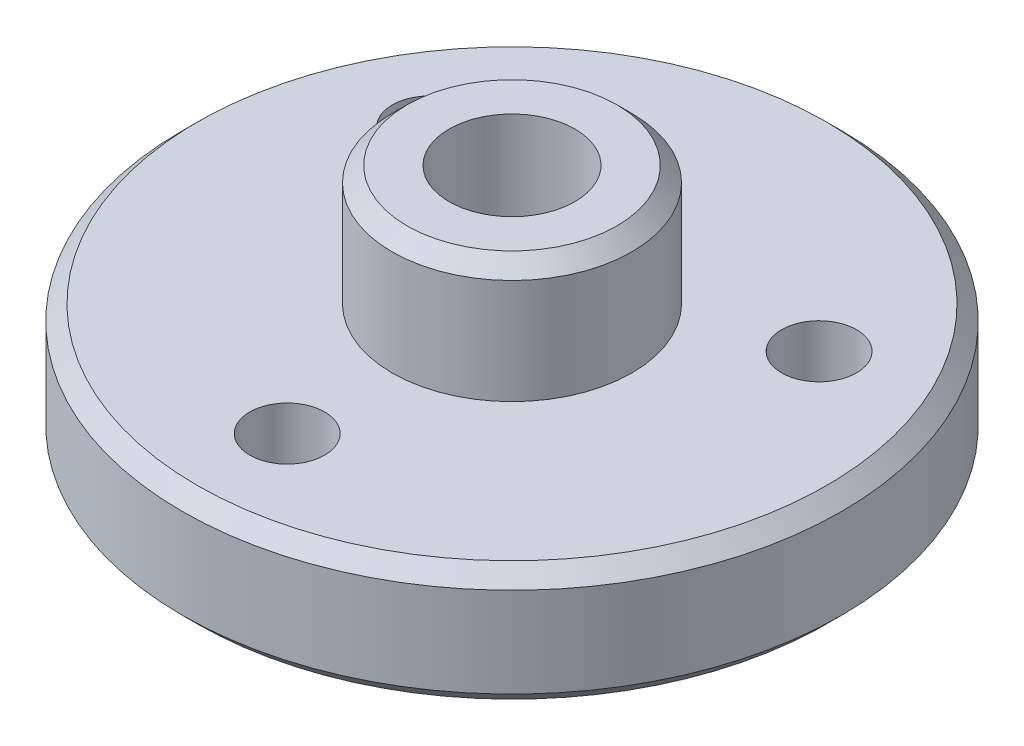
SolidWorks part; units mm, degrees
material "6061 合金"
ref_plane "前视基准面" through (0, 0, 0) normal (0, 0, 1) x (1, 0, 0)
ref_plane "上视基准面" through (0, 0, 0) normal (0, 1, 0) x (1, 0, 0)
ref_plane "右视基准面" through (0, 0, 0) normal (1, 0, 0) x (0, 0, -1)
sketch "草图1" plane through (0, 0, 0) normal (0, 0, 1) x (1, 0, 0)
  line L0 (0, 8) -> (0, 0)
  line L1 (0, 0) -> (3, 0)
  line L2 (4, -0.9) -> (4, 0)
  line L3 (4, 0) -> (11, 0)
  line L4 (11, 0) -> (11, 4)
  line L5 (11, 4) -> (4, 4)
  line L6 (4, 4) -> (4, 8)
  line L7 (4, 8) -> (0, 8)
  line L8 (0, 0) -> (0, -13.1272) construction
  line L9 (3, 0) -> (3, -0.9)
  line L10 (3, -0.9) -> (4, -0.9)
  dimension "D1" = 8
  dimension "D2" = 8
  dimension "D3" = 22
  dimension "D4" = 0.9
  dimension "D5" = 4
  dimension "D6" = 4
  dimension "D7" = 6
revolve "旋转1" add sketch "草图1" angle 360 about L8
hole_wizard "M3 螺纹孔1" positions "草图2" profile "草图3" tap size "M3" standard "GB" end condition through all
sketch "草图2" plane through (0, 4, 0) normal (0, 1, 0) x (1, 0, 0)
  circle A0 centre (0, 0) radius 7.5 construction
  point P0 (-6.4952, 3.75)
  point P11 (6.4952, 3.75)
  point P12 (0, -7.5)
  dimension "D1" = 15
  dimension "D2" = 3
sketch "草图3" plane through (-6.4952, 4, -3.75) normal (1, 0, 0) x (0, 0, 1)
  line L0 (0, 0) -> (0, 4.9)
  line L1 (0, 4.9) -> (1.25, 4.9)
  line L2 (1.25, 4.9) -> (1.25, 0)
  line L5 (1.25, 0) -> (0, 0)
  line L11 (0, -6.35) -> (0, 107.95) construction
  dimension "通孔螺纹孔钻头直径" = 2.5
  dimension "通孔螺纹孔钻头深度" = 4.9
cosmetic thread "孔螺蚊线2" parameters "D2"=3
cosmetic thread "孔螺蚊线3" parameters "D2"=3
cosmetic thread "孔螺蚊线4" parameters "D2"=3
hole_wizard "M5 螺纹孔1" positions "草图4" profile "草图5" tap size "M5" standard "GB" end condition through all
sketch "草图4" plane through (0, 0, 0) normal (0, -1, 0) x (-1, 0, 0)
  point P0 (0, 0)
sketch "草图5" plane through (0, 0, 0) normal (1, 0, 0) x (0, 0, -1)
  line L0 (0, 0) -> (0, 8)
  line L1 (0, 8) -> (2.1, 8)
  line L2 (2.1, 8) -> (2.1, 0)
  line L5 (2.1, 0) -> (0, 0)
  line L11 (0, -6.35) -> (0, 107.95) construction
  dimension "通孔螺纹孔钻头直径" = 4.2
  dimension "通孔螺纹孔钻头深度" = 8
cosmetic thread "孔螺蚊线5" parameters "D2"=5
chamfer "倒角1" distance 0.5 angle 45 4 edges at (0, 0, 11) (0, 4, 11) (0, 8, 4) (0, 0, 4)
